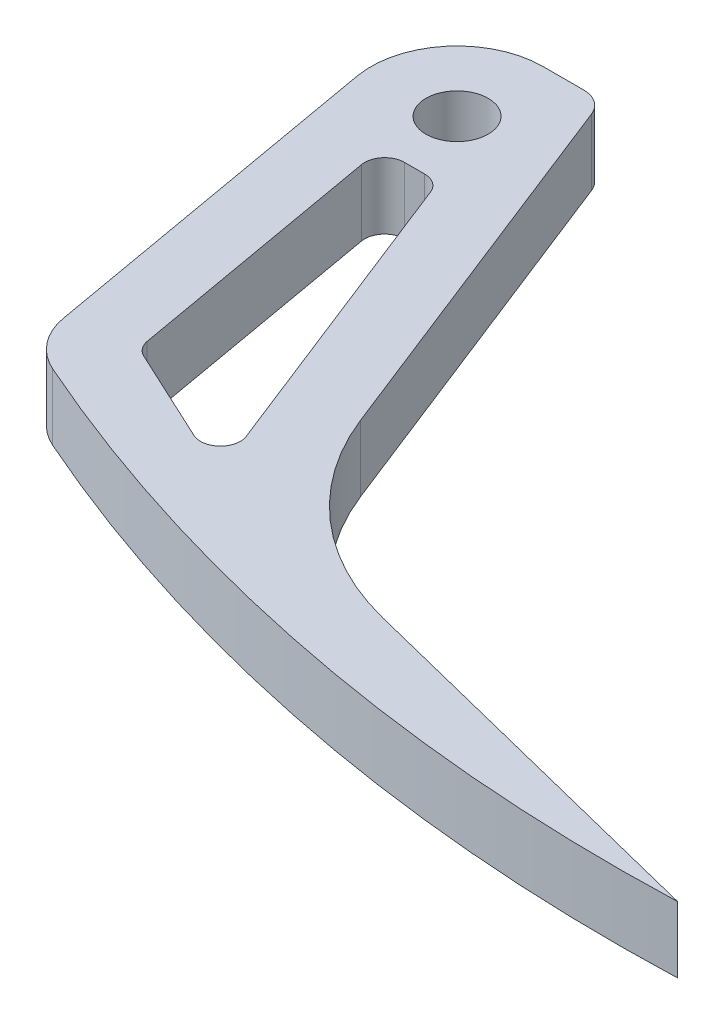
SolidWorks part; units mm, degrees
ref_plane "Front Plane" through (0, 0, 0) normal (0, 0, 1) x (1, 0, 0)
ref_plane "Top Plane" through (0, 0, 0) normal (0, 1, 0) x (1, 0, 0)
ref_plane "Right Plane" through (0, 0, 0) normal (1, 0, 0) x (0, 0, -1)
other "Bounding Box"
ref_plane "Default Plane" through (13.8565, 3.175, 6.7999) normal (0, -1, 0) x (-1, 0, 0)
sketch "Sketch1" plane through (0, 0, 0) normal (0, 1, 0) x (1, 0, 0)
  line L0 (5.6242, 8.255) -> (25.4, -42.037)
  line L1 (25.4, -42.037) -> (76.2, -54.737)
  line L2 (76.2, -54.737) -> (14.0408, -47.7166) construction
  line L5 (-8.1296, -1.4335) -> (-1.5136, -38.9546)
  line L6 (-1.5136, -38.9546) -> (14.0408, -47.7166) construction
  line L7 (0, 8.255) -> (5.6242, 8.255)
  line L8 (14.0408, -47.7166) -> (25.4, -42.037) construction
  line L9 (0, 0) -> (19.7204, -44.8768) construction
  line L10 (19.7204, -44.8768) -> (76.2, -54.737) construction
  line L11 (0, 0) -> (0, -54.737) construction
  line L12 (0, -54.737) -> (76.2, -54.737) construction
  line L13 (76.2, -54.737) -> (69.85, -54.737)
  circle A0 centre (0, 0) radius 2.9845
  arc A1 (7.8943, 2.4135) -> (7.6824, 3.0209) centre (0, 0) ccw construction
  arc A2 (7.8943, 2.4135) -> (7.6824, 3.0209) centre (0, 0) ccw
  arc A3 (0, 8.255) -> (-8.1296, -1.4335) centre (0, 0) ccw construction
  arc A4 (0, 8.255) -> (-8.1296, -1.4335) centre (0, 0) ccw
  arc A6 (-1.5136, -38.9546) -> (75.7838, -54.6329) centre (69.85, 114.4977) ccw
  dimension "D1" = 5.969
  dimension "D8" = 8.255
  dimension "D2" = 12.7
  dimension "D3" = 54.737
  dimension "D4" = 76.2
  dimension "D5" = 12.7
  dimension "D6" = 25.4
  dimension "D7" = 6.35
  dimension "D9" = 10
  dimension "D10" = 38.1
extrude "Boss-Extrude1" add sketch "Sketch1" along normal blind 6.35
sketch "Sketch2" plane through (0, 6.35, 0) normal (0, 1, 0) x (1, 0, 0)
  line L1 (4.0073, -34.5191) -> (18.2195, -41.1285)
  line L2 (18.2195, -41.1285) -> (4.5439, -6.35)
  line L3 (4.5439, -6.35) -> (4.5439, 0) construction
  line L4 (0, 0) -> (18.2195, 0) construction
  line L5 (18.2195, 0) -> (18.2195, -41.1285) construction
  line L6 (-0.9596, -6.35) -> (4.5439, -6.35)
  line L8 (4.0073, -34.5191) -> (-0.9596, -6.35)
  line L9 (-8.1296, -1.4335) -> (-1.5136, -38.9546) construction
  line L10 (5.6242, 8.255) -> (25.4, -42.037) construction
  line L12 (-1.5136, -38.9546) -> (18.385, -48.2086) construction
  line L13 (11.3817, -23.7392) -> (17.2912, -21.4155) construction
  line L14 (1.5239, -20.4345) -> (-4.8216, -20.1941) construction
  line L15 (8.4357, -43.5816) -> (11.1134, -37.8238) construction
  line L16 (0, 0) -> (0, -6.35) construction
  arc A1 (-1.5136, -38.9546) -> (75.7838, -54.6329) centre (69.85, 114.4977) ccw construction
  dimension "D1" = 6.35
  dimension "D2" = 6.35
extrude "Cut-Extrude1" cut sketch "Sketch2" against normal through all
fillet "Fillet1" radius 25.4 1 edges at (25.4, 3.175, 42.037)
fillet "Fillet2" radius 6.35 1 edges at (-1.5136, 3.175, 38.9546)
fillet "Fillet3" radius 1.905 4 edges at (4.0073, 3.175, 34.5191) (18.2195, 3.175, 41.1285) (4.5439, 3.175, 6.35) (-0.9596, 3.175, 6.35)
fillet "Fillet4" radius 2.54 1 edges at (5.6242, 3.175, -8.255)
sketch "Sketch3" [suppressed] plane through (0, 6.35, 0) normal (0, 1, 0) x (1, 0, 0)
  line L0 (1.9469, 8.255) -> (8.8703, 8.255)
  line L1 (0, 8.255) -> (3.8937, 8.255) construction
  line L2 (8.8703, 8.255) -> (8.8703, 0)
  line L3 (6.2575, 6.6445) -> (20.613, -29.863) construction
  line L4 (8.8703, 0) -> (1.9469, 8.255)
extrude "Boss-Extrude2" [suppressed] add sketch "Sketch3" against normal through all
fillet "Fillet5" [suppressed] radius 1.27
fillet "Fillet6" [suppressed] radius 12.7
